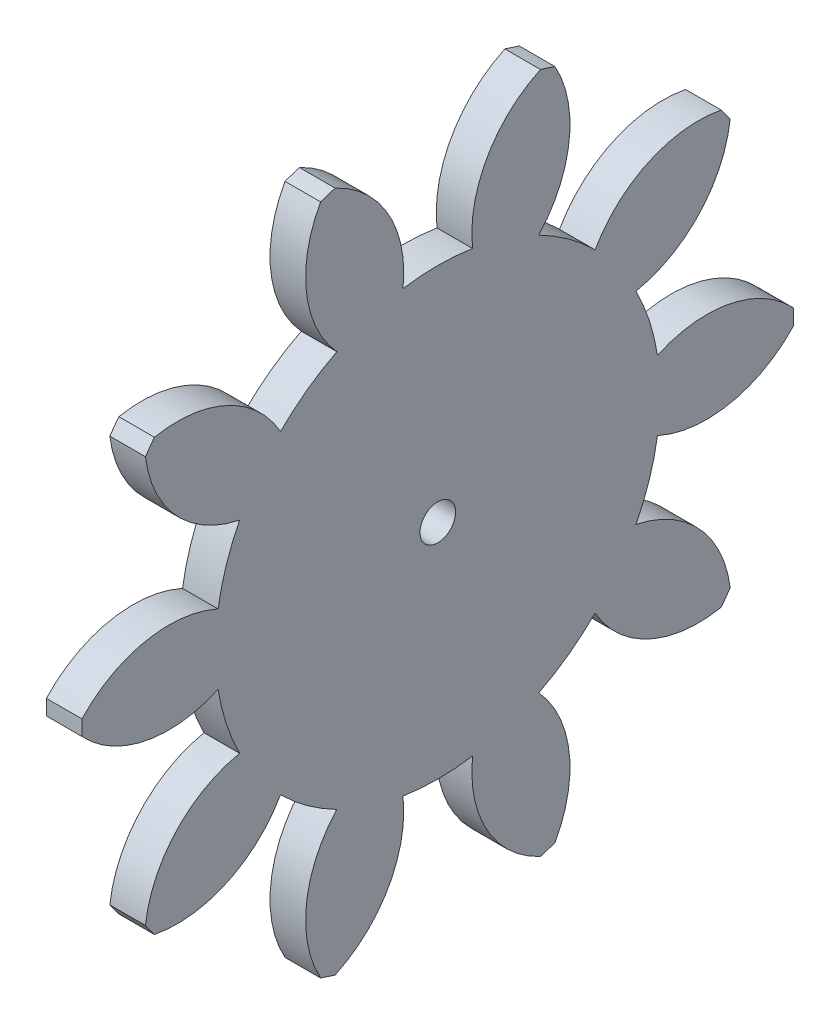
SolidWorks part; units mm, degrees
ref_plane "Plane1" through (0, 0, 0) normal (0, 0, 1) x (1, 0, 0)
ref_plane "Plane2" through (0, 0, 0) normal (0, 1, 0) x (1, 0, 0)
ref_plane "Plane3" through (0, 0, 0) normal (1, 0, 0) x (0, 0, -1)
sketch "HoldingSke" plane through (0, 0, 0) normal (0, 1, 0) x (1, 0, 0)
  line L0 (0, 0) -> (0.197, -0.0347)
  line L1 (-15, 0) -> (100, 0) construction
  line L2 (0, 0) -> (-2.1039, 2.3779)
  line L3 (0, 0) -> (-11.863, 4.5341)
  line L4 (0, 0) -> (8.5048, 1.4996)
  line L5 (0, 0) -> (-46.8476, -17.4728)
  line L6 (0, 0) -> (-2.4869, -1.6779)
  line L7 (-2.1039, 2.3779) -> (8.6586, 51.2059)
  line L8 (-76.2, 54.61) -> (-75.7, 54.61)
  line L9 (-71.009, 38.7566) -> (-53.1078, 45.2721)
  line L10 (-76.2, 71.12) -> (104.1128, 71.12)
  line L11 (0, 0) -> (-3, 0)
  line L12 (-76.2, 101.6) -> (-76.033, 101.6)
  line L13 (24.9733, 27.94) -> (52.9518, 28.4284)
  line L14 (24.9733, 27.94) -> (24.9743, 27.94)
  line L15 (24.9733, 27.94) -> (100.4006, 29.5858)
  line L16 (-63.627, -5) -> (-12.827, -5)
  circle A0 centre (0, 0) radius 1.5
  circle A1 centre (0, 0) radius 18.749
  circle A2 centre (0, 0) radius 37.5
  circle A3 centre (0, 0) radius 1.5
  dimension "MHD" = 37.498
  dimension "Hub_dia" = 75
  dimension "Bore" = 3
  dimension "MBD" = 3
  dimension "Num_teeth" = 10
  dimension "Pitch" = 0.2
  dimension "Overall_len" = 50
  dimension "Show_teeth" = 10
  dimension "Thickness" = 3
  dimension "OAL" = 50.0001
  dimension "T_dim" = 0.5
  dimension "Ap" = 20
  dimension "H" = 19.05
  dimension "Pitch_radius" = 180.3128
  dimension "Width" = 3
  dimension "Backlash" = 0.167
  dimension "Addendum_fac" = 1
  dimension "Dedendum_fac" = 1.25
  dimension "Clearance_fac" = 0.25
  dimension "Dedendum_add" = 0.001
  dimension "Module" = 5
sketch "BasProSke" plane through (0, 0, 0) normal (0, 1, 0) x (1, 0, 0)
  line L0 (-10, 0) -> (60, 0) construction
  line L1 (0, 0) -> (0, 30)
  line L2 (0, 0) -> (3, 0)
  line L3 (3, 0) -> (3, 30)
  line L4 (3, 30) -> (0, 30)
  dimension "Thickness" = 3
  dimension "Diameter" = 60
revolve "Base-Revolve" add sketch "BasProSke" angle 360 about L0
sketch "TooCutSke" plane through (0, 0, 0) normal (1, 0, 0) x (0, 0, -1)
  line L1 (0, 0) -> (0, 107) construction
  line L2 (0, 0) -> (-4.2026, 24.6442) construction
  line L3 (0, 0) -> (-15.2881, 47.0521) construction
  line L4 (-4.2026, 24.6442) -> (-7.6441, 23.526) construction
  arc A0 (2.9333, 18.5181) -> (-2.9333, 18.5181) centre (0, 0) ccw
  arc A1 (8.6913, 28.74) -> (-8.6913, 28.74) centre (0, 0) ccw
  circle A2 centre (0, 0) radius 25 construction
  circle A3 centre (0, 0) radius 23.4923 construction
  arc A4 (-2.9333, 18.5181) -> (-8.6913, 28.74) centre (-12.8686, 19.6542) ccw
  arc A5 (8.6913, 28.74) -> (2.9333, 18.5181) centre (12.8686, 19.6542) ccw
  dimension "Root_dia" = 37.498
  dimension "Overcut_dia" = 60.0508
  dimension "Pitch_dia" = 50
  dimension "Base_dia" = 46.9846
  dimension "Flank_rad" = 10
  dimension "Half_ang" = 18
  dimension "Half_CT" = 3.6186
extrude "ToothCut" cut sketch "TooCutSke" along normal through all
fillet "Breaks" [suppressed] radius 0.1
fillet "RootFillets" [suppressed] radius 1.251
pattern_circular "TeethCuts" count 10 every 36 about axis through (-10, 0, 0) along (1, 0, 0) of "ToothCut", "RootFillets", "Breaks"
sketch "HubNeaOneSke" plane through (0, 0, 0) normal (-1, 0, 0) x (0, 0, 1)
  circle A0 centre (0, 0) radius 18.749
  dimension "Diameter" = 37.498
extrude "HubNearOne" [suppressed] add sketch "HubNeaOneSke" along normal blind 47.0001
sketch "HubNeaBotSke" plane through (0, 0, 0) normal (-1, 0, 0) x (0, 0, 1)
  circle A0 centre (0, 0) radius 18.749
  dimension "Diameter" = 37.498
extrude "HubNearBoth" [suppressed] add sketch "HubNeaBotSke" along normal blind 23.5
ref_plane "FarPln" through (3, 0, 0) normal (1, 0, 0) x (0, 0, -1)
sketch "HubFarSke" plane through (3, 0, 0) normal (1, 0, 0) x (0, 0, -1)
  circle A0 centre (0, 0) radius 18.749
  dimension "Diameter" = 37.498
extrude "HubFar" [suppressed] add sketch "HubFarSke" along normal blind 23.5
sketch "BorSke" plane through (0, 0, 0) normal (1, 0, 0) x (0, 0, -1)
  circle A0 centre (0, 0) radius 1.5
  dimension "Diameter" = 3
extrude "Bore" cut sketch "BorSke" along normal mid plane 100.0001
sketch "KeySke" plane through (0, 0, 0) normal (1, 0, 0) x (0, 0, -1)
  line L0 (-0.6, 0) -> (-0.6, 2)
  line L1 (-0.6, 2) -> (0.6, 2)
  line L2 (0.6, 2) -> (0.6, 0)
  line L3 (0, 0) -> (0, 34) construction
  line L4 (-0.6, 0) -> (0.6, 0)
  dimension "Offset" = 2
  dimension "Width" = 1.2
extrude "Keyway" [suppressed] cut sketch "KeySke" along normal mid plane 100.0001
pattern_circular "Keyway2" [suppressed] count 2 every 90 about axis through (-10, 0, 0) along (1, 0, 0)
equation "' \"Module@HoldingSke\" = 6.35"
equation "' \"Num_teeth@HoldingSke\" = 12"
equation "' \"Ap@HoldingSke\" =  20"
equation "' \"Ap@HoldingSke\" = 20"
equation "' \"Width@HoldingSke\" = 0.5 * 25.4"
equation "' \"Hub_dia@HoldingSke\"= 1 * 25.4"
equation "' \"Hub_dia@HoldingSke\" = 1 * 25.4"
equation "' \"Overall_len@HoldingSke\" = 1.0 * 25.4"
equation "' \"Bore@HoldingSke\" = 0.75 * 25.4"
equation "' \"T_dim@HoldingSke\" = 0.1 * 25.4"
equation "' \"Width@KeySke\" = 0.25 * 25.4"
equation "' \"Show_teeth@HoldingSke\" = 13"
equation "' \"Backlash@HoldingSke\" = 0.009 * 25.4"
equation "' \"Addendum_fac@HoldingSke\" = 1.0"
equation "' \"Dedendum_fac@HoldingSke\" = 1.25"
equation "' \"Dedendum_add@HoldingSke\" = 0.00005 * 25.4"
equation "' \"Clearance_fac@HoldingSke\" = 0.25"
equation "\"Pitch@HoldingSke\" = 1 / \"Module@HoldingSke\""
equation "\"Overcut_dia@TooCutSke\" = (\"Num_teeth@HoldingSke\" + 2 * \"Addendum_fac@HoldingSke\") / \"Pitch@HoldingSke\" + 0.002 * 25.4"
equation "\"Pitch_dia@TooCutSke\" = \"Num_teeth@HoldingSke\" / \"Pitch@HoldingSke\""
equation "\"Base_dia@TooCutSke\" = \"Num_teeth@HoldingSke\" / \"Pitch@HoldingSke\" * cos((\"Ap@HoldingSke\"  * 3.14159265 / 180))"
equation "\"Root_dia@TooCutSke\" = (\"Num_teeth@HoldingSke\" + 2) / \"Pitch@HoldingSke\" - 2 * (\"Addendum_fac@HoldingSke\" + \"Dedendum_fac@HoldingSke\") / \"Pitch@HoldingSke\" - \"Dedendum_add@HoldingSke\" * 2"
equation "\"Half_ang@TooCutSke\" = 180 / \"Num_teeth@HoldingSke\""
equation "\"Half_CT@TooCutSke\" = \"Num_teeth@HoldingSke\" / \"Pitch@HoldingSke\" * sin((3.14159265 / 2 / \"Num_teeth@HoldingSke\")) / 2 - 7 * \"Backlash@HoldingSke\" / 4"
equation "\"Flank_rad@TooCutSke\" = \"Num_teeth@HoldingSke\" / \"Pitch@HoldingSke\" / 5"
equation "\"Radius@RootFillets\" = \"Clearance_fac@HoldingSke\" / \"Pitch@HoldingSke\" + \"Dedendum_add@HoldingSke\""
equation "\"Break_rad@Breaks\" = 0.02 / \"Pitch@HoldingSke\""
equation "\"Thickness@HoldingSke\" = \"Width@HoldingSke\""
equation "\"OAL@HoldingSke\" = \"Thickness@HoldingSke\""
equation "\"MHD@HoldingSke\" = (\"Num_teeth@HoldingSke\" + 2) / \"Pitch@HoldingSke\" - 2 * (\"Addendum_fac@HoldingSke\" + \"Dedendum_fac@HoldingSke\")  / \"Pitch@HoldingSke\" - \"Dedendum_add@HoldingSke\" * 2"
equation "\"MBD@HoldingSke\" = (\"Num_teeth@HoldingSke\" + 2) / \"Pitch@HoldingSke\" - 2 * (\"Addendum_fac@HoldingSke\" + \"Dedendum_fac@HoldingSke\")  / \"Pitch@HoldingSke\" - \"Dedendum_add@HoldingSke\" * 2 - 0.002 * 25.4"
equation "\"MHD@HoldingSke\" = ((sgn( \"MHD@HoldingSke\" - \"Hub_dia@HoldingSke\" )-1)*( \"MHD@HoldingSke\" - \"Hub_dia@HoldingSke\" ))/-2+ \"Hub_dia@HoldingSke\""
equation "\"MBD@HoldingSke\" = ((sgn( \"MBD@HoldingSke\" - \"Bore@HoldingSke\" )-1)*( \"MBD@HoldingSke\" - \"Bore@HoldingSke\" ))/-2+ \"Bore@HoldingSke\""
equation "\"OAL@HoldingSke\" = ((sgn( \"OAL@HoldingSke\" - \"Overall_len@HoldingSke\" )+1)*( \"OAL@HoldingSke\" - \"Overall_len@HoldingSke\" ))/2 + \"Overall_len@HoldingSke\" + 0.000002 * 25.4"
equation "\"Num_teeth@TeethCuts\" = int( \"Show_teeth@HoldingSke\" ) + 1"
equation "\"Num_teeth@TeethCuts\" = ((sgn( \"Num_teeth@TeethCuts\" - \"Num_teeth@HoldingSke\" )-1)*( \"Num_teeth@TeethCuts\" - \"Num_teeth@HoldingSke\" ))/-2+ \"Num_teeth@HoldingSke\""
equation "\"Num_teeth@TeethCuts\" = ((sgn( \"Num_teeth@TeethCuts\" - 2.0)+1)*( \"Num_teeth@TeethCuts\" - 2.0))/2 +2.0"
equation "\"Angle@TeethCuts\" = 360.0 / \"Num_teeth@HoldingSke\""
equation "\"Diameter@BasProSke\" = (\"Num_teeth@HoldingSke\" + 2 * \"Addendum_fac@HoldingSke\") / \"Pitch@HoldingSke\""
equation "\"Thickness@BasProSke\"  = \"Thickness@HoldingSke\""
equation "' \"Fillet_rad@BasProSke\" =  \"Thickness@HoldingSke\" * 0.05"
equation "' \"Fillet_rad@BasProSke\" = \"Thickness@HoldingSke\" * 0.05"
equation "\"MHD@HoldingSke\" = ((sgn( \"MHD@HoldingSke\" - \"Root_dia@TooCutSke\" )-1)*( \"MHD@HoldingSke\" - \"Root_dia@TooCutSke\" ))/-2+ \"Root_dia@TooCutSke\""
equation "\"Diameter@HubNeaOneSke\" = \"MHD@HoldingSke\""
equation "\"Length@HubNearOne\" = \"OAL@HoldingSke\" - \"Thickness@BasProSke\""
equation "\"Diameter@HubNeaBotSke\" = \"MHD@HoldingSke\""
equation "\"Length@HubNearBoth\" = ( \"OAL@HoldingSke\" - \"Thickness@BasProSke\" ) / 2.0"
equation "\"Thickness@FarPln\" = \"Thickness@BasProSke\""
equation "\"Diameter@HubFarSke\" = \"MHD@HoldingSke\""
equation "\"Length@HubFar\" = ( \"OAL@HoldingSke\" - \"Thickness@BasProSke\" ) / 2.0"
equation "\"Diameter@BorSke\" = \"MBD@HoldingSke\""
equation "\"D1@Bore\" = \"OAL@HoldingSke\" * 2.0"
equation "\"D1@Keyway\" = \"OAL@HoldingSke\" * 2.0"
equation "\"Offset@KeySke\" = \"T_dim@HoldingSke\" + \"MBD@HoldingSke\" / 2.0"
